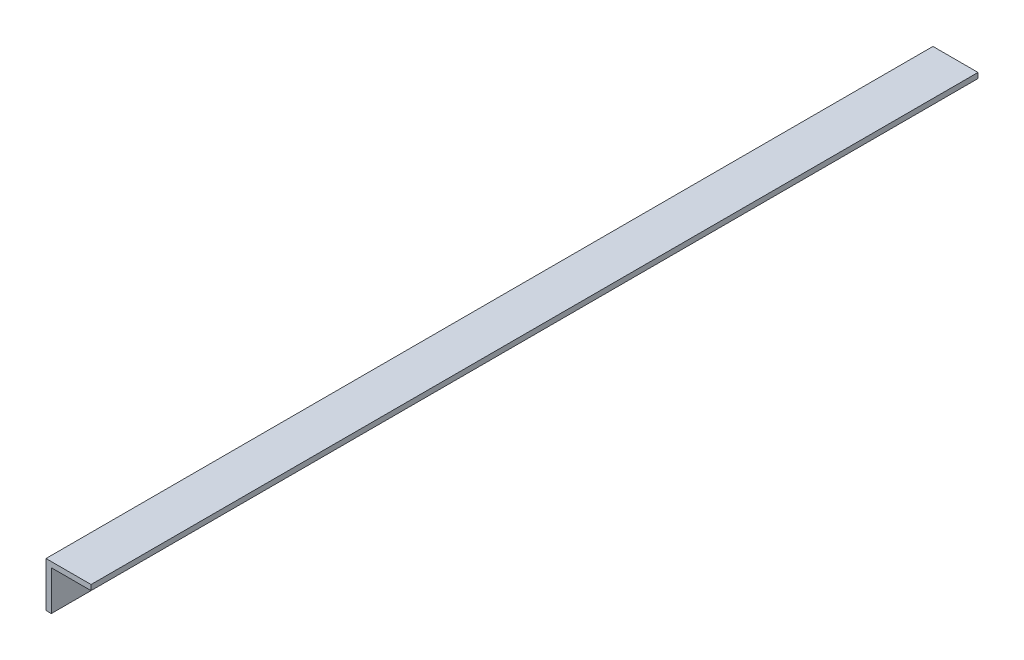
SolidWorks part; units mm, degrees
material "6061 Alloy"
ref_plane "Front Plane" through (0, 0, 0) normal (0, 0, 1) x (1, 0, 0)
ref_plane "Top Plane" through (0, 0, 0) normal (0, 1, 0) x (1, 0, 0)
ref_plane "Right Plane" through (0, 0, 0) normal (1, 0, 0) x (0, 0, -1)
sketch "Sketch1" plane through (0, 0, 0) normal (0, 0, 1) x (1, 0, 0)
  line L0 (0, 0) -> (0, -25.4)
  line L1 (0, 0) -> (25.4, 0)
  line L2 (3, -3) -> (3, -25.4)
  line L3 (3, -3) -> (25.4, -3)
  line L4 (25.4, 0) -> (25.4, -3)
  line L5 (0, -25.4) -> (3, -25.4)
  dimension "D1" = 25.4
  dimension "D2" = 3
  dimension "D3" = 25.4
extrude "Boss-Extrude1" add sketch "Sketch1" along normal blind 500
